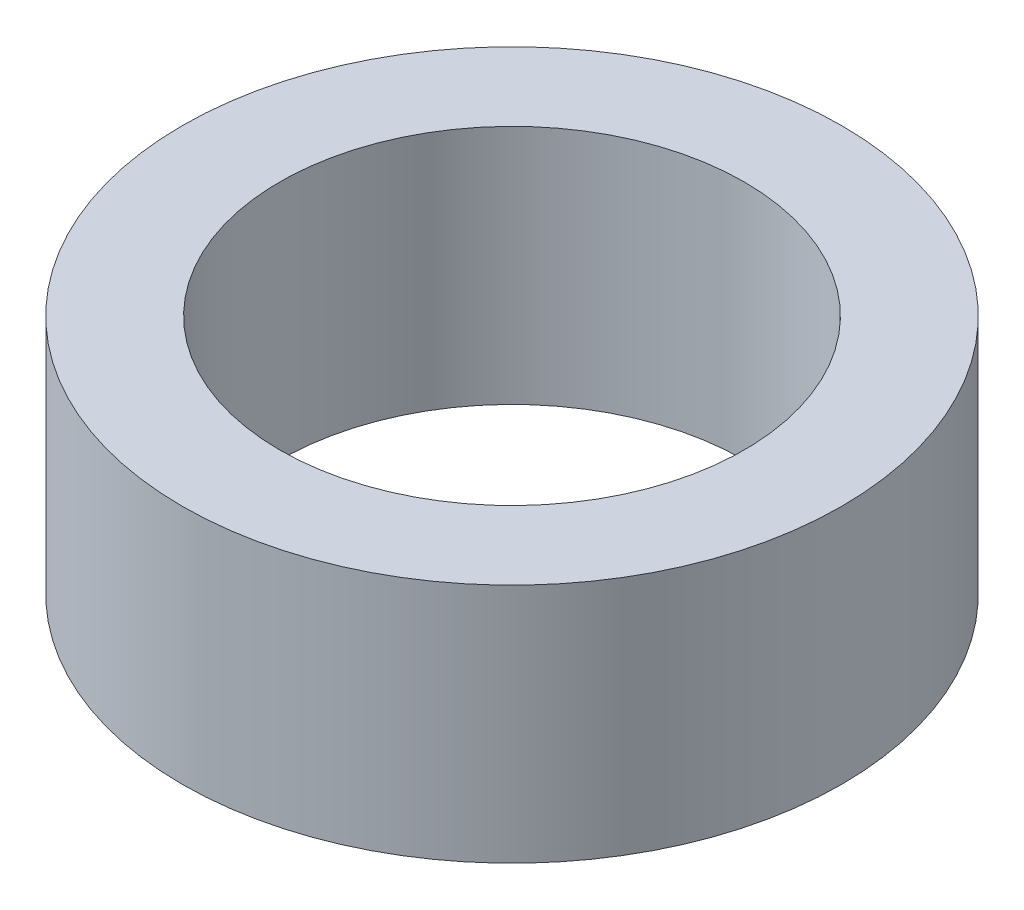
SolidWorks part; units mm, degrees
ref_plane "Front Plane" through (0, 0, 0) normal (0, 0, 1) x (1, 0, 0)
ref_plane "Top Plane" through (0, 0, 0) normal (0, 1, 0) x (1, 0, 0)
ref_plane "Right Plane" through (0, 0, 0) normal (1, 0, 0) x (0, 0, -1)
sketch "Sketch1" plane through (0, 0, 0) normal (0, 1, 0) x (1, 0, 0)
  circle A0 centre (0, 0) radius 40.5
  circle A1 centre (0, 0) radius 57.5
  dimension "D1" = 81
  dimension "D2" = 115
extrude "Boss-Extrude1" add sketch "Sketch1" along normal blind 42
